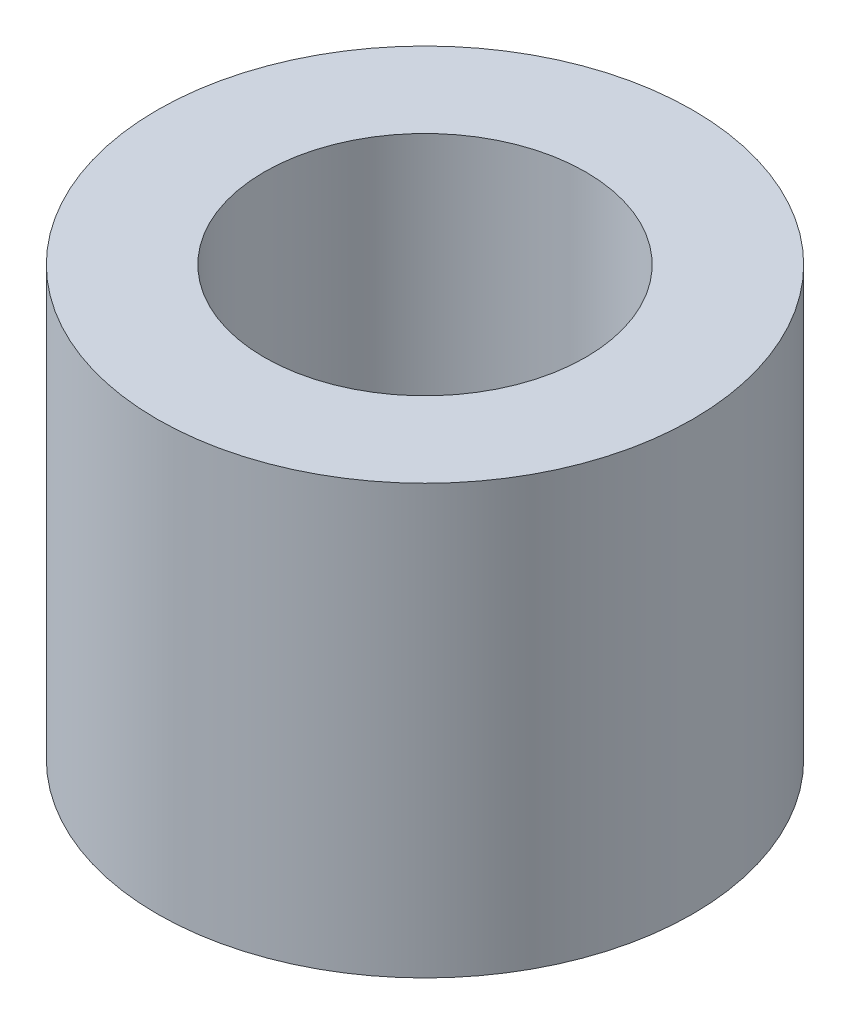
SolidWorks part; units mm, degrees
ref_plane "Front Plane" through (0, 0, 0) normal (0, 0, 1) x (1, 0, 0)
ref_plane "Top Plane" through (0, 0, 0) normal (0, 1, 0) x (1, 0, 0)
ref_plane "Right Plane" through (0, 0, 0) normal (1, 0, 0) x (0, 0, -1)
sketch "Sketch1" plane through (0, 0, 0) normal (0, 1, 0) x (1, 0, 0)
  circle A0 centre (0, 0) radius 1.5
  circle A1 centre (0, 0) radius 2.5
  dimension "D1" = 3
  dimension "D2" = 1
extrude "Boss-Extrude1" add sketch "Sketch1" along normal blind 4
